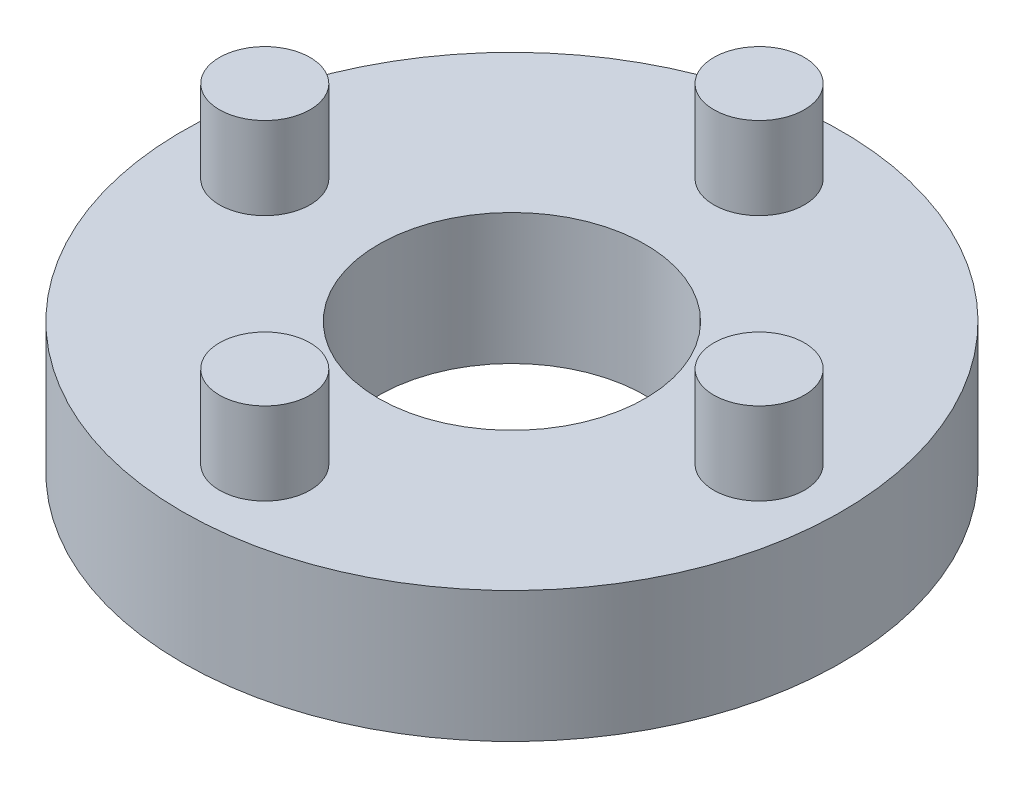
SolidWorks part; units mm, degrees
material "ABS"
ref_plane "Front Plane" through (0, 0, 0) normal (0, 0, 1) x (1, 0, 0)
ref_plane "Top Plane" through (0, 0, 0) normal (0, 1, 0) x (1, 0, 0)
ref_plane "Right Plane" through (0, 0, 0) normal (1, 0, 0) x (0, 0, -1)
sketch "Sketch1" plane through (0, 0, 0) normal (0, 1, 0) x (1, 0, 0)
  circle A0 centre (0, 0) radius 3.2385
  circle A1 centre (0, 0) radius 8
  dimension "D1" = 6.477
  dimension "D2" = 16
extrude "Boss-Extrude1" add sketch "Sketch1" along normal blind 3.175
sketch "Sketch2" plane through (0, 3.175, 0) normal (0, 1, 0) x (1, 0, 0)
  circle A0 centre (0, 6) radius 1.1
  circle A1 centre (0, 0) radius 3.2385 construction
  circle A2 centre (6, 0) radius 1.1
  circle A3 centre (0, -6) radius 1.1
  circle A4 centre (-6, 0) radius 1.1
  point P13 (0, 0)
  dimension "D2" = 2.2
  dimension "D1" = 6
  dimension "D3" = 4
extrude "Boss-Extrude2" add sketch "Sketch2" along normal blind 2
